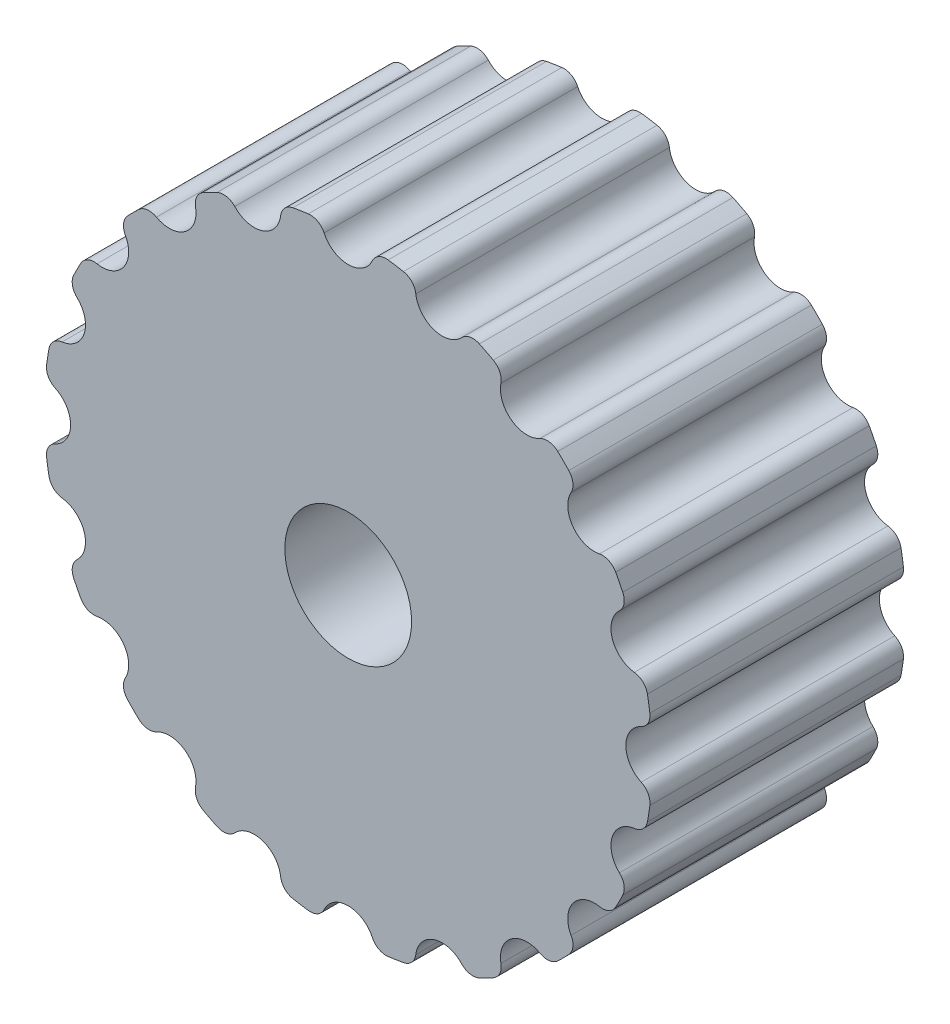
SolidWorks part; units mm, degrees
ref_plane "Front Plane" through (0, 0, 0) normal (0, 0, 1) x (1, 0, 0)
ref_plane "Top Plane" through (0, 0, 0) normal (0, 1, 0) x (1, 0, 0)
ref_plane "Right Plane" through (0, 0, 0) normal (1, 0, 0) x (0, 0, -1)
sketch "Sketch1" plane through (0, 0, 0) normal (0, 0, 1) x (1, 0, 0)
  circle A0 centre (0, 0) radius 12
  circle A1 centre (0, 0) radius 2.5
  dimension "D1" = 5
  dimension "D2" = 24
extrude "Boss-Extrude1" add sketch "Sketch1" along normal blind 10
sketch "Sketch2" plane through (0, 0, 10) normal (0, 0, 1) x (1, 0, 0)
  line L0 (0, 0) -> (0, 12) construction
  circle A0 centre (0, 0) radius 12 construction
  circle A1 centre (0, 12) radius 1.05
  circle A2 centre (3.7082, 11.4127) radius 1.05
  circle A3 centre (7.0534, 9.7082) radius 1.05
  circle A4 centre (9.7082, 7.0534) radius 1.05
  circle A5 centre (11.4127, 3.7082) radius 1.05
  circle A6 centre (12, 0) radius 1.05
  circle A7 centre (11.4127, -3.7082) radius 1.05
  circle A8 centre (9.7082, -7.0534) radius 1.05
  circle A9 centre (7.0534, -9.7082) radius 1.05
  circle A10 centre (3.7082, -11.4127) radius 1.05
  circle A11 centre (0, -12) radius 1.05
  circle A12 centre (-3.7082, -11.4127) radius 1.05
  circle A13 centre (-7.0534, -9.7082) radius 1.05
  circle A14 centre (-9.7082, -7.0534) radius 1.05
  circle A15 centre (-11.4127, -3.7082) radius 1.05
  circle A16 centre (-12, 0) radius 1.05
  circle A17 centre (-11.4127, 3.7082) radius 1.05
  circle A18 centre (-9.7082, 7.0534) radius 1.05
  circle A19 centre (-7.0534, 9.7082) radius 1.05
  circle A20 centre (-3.7082, 11.4127) radius 1.05
  point P48 (0, 0)
  dimension "D1" = 2.1
  dimension "D2" = 20
extrude "Cut-Extrude1" cut sketch "Sketch2" against normal blind 10
fillet "Fillet1" radius 0.6 40 edges at (-1.049, 11.9541, 5) (1.049, 11.9541, 5) (2.6964, 11.6931, 5) (4.6917, 11.0448, 5) (6.1778, 10.2876, 5) (7.8751, 9.0545, 5) (9.0545, 7.8751, 5) (10.2876, 6.1778, 5) (11.0448, 4.6917, 5) (11.6931, 2.6964, 5) (11.9541, 1.049, 5) (11.9541, -1.049, 5) (11.6931, -2.6964, 5) (11.0448, -4.6917, 5) (10.2876, -6.1778, 5) (9.0545, -7.8751, 5) (7.8751, -9.0545, 5) (6.1778, -10.2876, 5) (4.6917, -11.0448, 5) (2.6964, -11.6931, 5) (1.049, -11.9541, 5) (-1.049, -11.9541, 5) (-2.6964, -11.6931, 5) (-4.6917, -11.0448, 5) (-6.1778, -10.2876, 5) (-7.8751, -9.0545, 5) (-9.0545, -7.8751, 5) (-10.2876, -6.1778, 5) (-11.0448, -4.6917, 5) (-11.6931, -2.6964, 5) (-11.9541, -1.049, 5) (-11.9541, 1.049, 5) (-11.6931, 2.6964, 5) (-11.0448, 4.6917, 5) (-10.2876, 6.1778, 5) (-9.0545, 7.8751, 5) (-7.8751, 9.0545, 5) (-6.1778, 10.2876, 5) (-4.6917, 11.0448, 5) (-2.6964, 11.6931, 5)
sketch "Sketch3" plane through (0, 0, 10) normal (0, 0, 1) x (1, 0, 0)
  line L0 (0, 0) -> (0, 34.3786) construction
